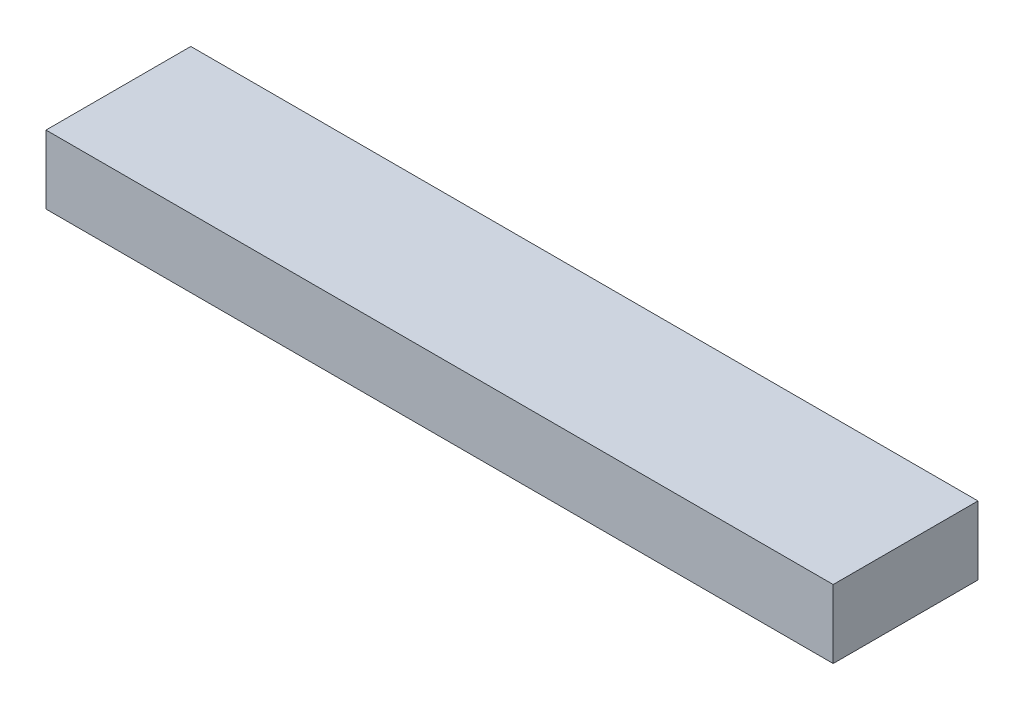
SolidWorks part; units mm, degrees
ref_plane "Front Plane" through (0, 0, 0) normal (0, 0, 1) x (1, 0, 0)
ref_plane "Top Plane" through (0, 0, 0) normal (0, 1, 0) x (1, 0, 0)
ref_plane "Right Plane" through (0, 0, 0) normal (1, 0, 0) x (0, 0, -1)
sketch "Sketch1" plane through (0, 0, 0) normal (0, 0, 1) x (1, 0, 0)
  line L1 (-149.5, -13) -> (149.5, -13)
  line L2 (-149.5, -13) -> (-149.5, 13)
  line L3 (-149.5, 13) -> (149.5, 13)
  line L4 (149.5, -13) -> (149.5, 13)
  line L5 (-149.5, -13) -> (149.5, 13) construction
  line L6 (-149.5, 13) -> (149.5, -13) construction
  point P0 (0, 0)
  dimension "D1" = 299
  dimension "D2" = 26
extrude "Boss-Extrude1" add sketch "Sketch1" along normal blind 55
